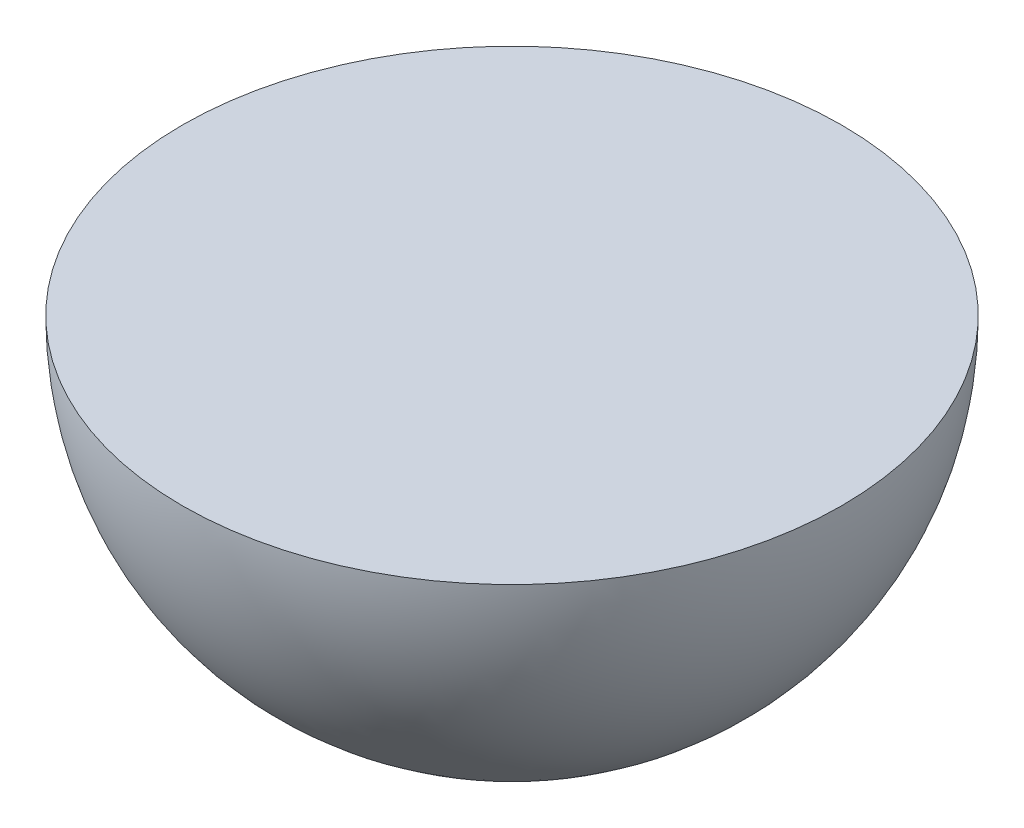
SolidWorks part; units mm, degrees
ref_plane "Front Plane" through (0, 0, 0) normal (0, 0, 1) x (1, 0, 0)
ref_plane "Top Plane" through (0, 0, 0) normal (0, 1, 0) x (1, 0, 0)
ref_plane "Right Plane" through (0, 0, 0) normal (1, 0, 0) x (0, 0, -1)
sketch "Sketch1" plane through (0, 0, 0) normal (0, 0, 1) x (1, 0, 0)
  line L0 (-4.8, 0) -> (0, 0)
  line L1 (0, 0) -> (0, -4.8)
  arc A0 (-4.8, 0) -> (0, -4.8) centre (0, 0) ccw
  dimension "D1" = 4.8
  dimension "D2" = 4.8
revolve "Revolve1" add sketch "Sketch1" angle 360 about L1
